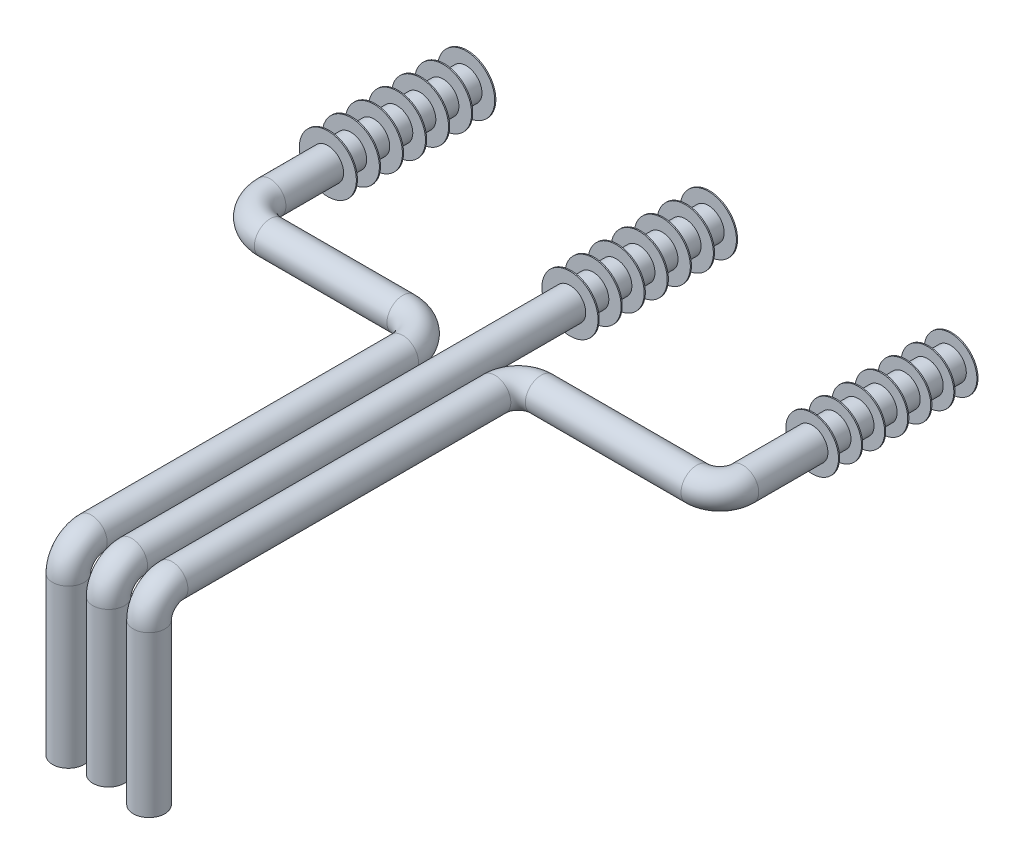
SolidWorks part; units mm, degrees
ref_plane "Alzado" through (0, 0, 0) normal (0, 0, 1) x (1, 0, 0)
ref_plane "Planta" through (0, 0, 0) normal (0, 1, 0) x (1, 0, 0)
ref_plane "Vista lateral" through (0, 0, 0) normal (1, 0, 0) x (0, 0, -1)
sketch "Croquis1" plane through (0, 0, 0) normal (0, 0, 1) x (1, 0, 0)
  line L0 (0, 0) -> (210, 0) construction
  line L1 (210, 0) -> (420, 0) construction
  circle A0 centre (0, 0) radius 13.7
  circle A1 centre (210, 0) radius 13.7
  circle A2 centre (210, 0) radius 13.7
  dimension "D1" = 27.4
  dimension "D3" = 27.4
  dimension "D2" = 210
  dimension "D4" = 210
sketch3d "Croquis3D1"
  line L0 (0, 0, 0) -> (0, 0, 170)
  line L1 (30, 0, 200) -> (145.0002, 0, 200)
  line L2 (175.0002, 0, 230) -> (175.0002, 0, 500)
  line L3 (175.0002, -20, 520) -> (175.0002, -156.8001, 520)
  arc A0 (0, 0, 170) -> (30, 0, 200) centre (30, 0, 170) ccw
  arc A1 (145.0002, 0, 200) -> (175.0002, 0, 230) centre (145.0002, 0, 230) ccw
  arc A2 (175.0002, 0, 500) -> (175.0002, -20, 520) centre (175.0002, -20, 500) ccw
  point P10 (0, 0, 200)
  point P11 (30, 30, 170)
  point P14 (175.0002, 0, 200)
  point P15 (145.0002, -30, 230)
  point P19 (175.0002, 0, 520)
  point P20 (195.0002, -20, 500)
  dimension "D1" = 30
  dimension "D2" = 20
  dimension "D3" = 175.0002
  dimension "D4" = 200
  dimension "D5" = 320
sweep "Barrer5" add path "Croquis3D1" circular profile diameter 27.4 parameters "D3"=27.4
sketch "Croquis14" plane through (0, 0, 0) normal (0, 0, 1) x (1, 0, 0)
  circle A0 centre (210, 0) radius 13.7
sketch3d "Croquis3D2"
  line L0 (210, 0, 0) -> (210, 0, 499.997)
  line L1 (210, -20, 519.997) -> (210, -153.4253, 519.997)
  arc A0 (210, 0, 499.997) -> (210, -20, 519.997) centre (210, -20, 499.997) ccw
  point P8 (210, 0, 519.997)
  point P9 (230, -20, 499.997)
  dimension "D1" = 20
  dimension "D2" = 519.997
sweep "Barrer6" add path "Croquis3D2" circular profile diameter 27.4 parameters "D3"=27.4
sketch "Croquis41" plane through (0, 0, 0) normal (0, 0, -1) x (-1, 0, 0)
  circle A0 centre (-420, 0) radius 13.7
  dimension "D1" = 27.4
sketch3d "Croquis3D3"
  line L0 (420, 0, 0) -> (420, 0, 180)
  line L1 (400, 0, 200) -> (264.998, 0, 200)
  line L2 (244.998, 0, 220) -> (244.998, 0, 500)
  line L3 (244.998, -20, 520) -> (244.998, -158.8149, 520)
  arc A0 (244.998, 0, 500) -> (244.998, -20, 520) centre (244.998, -20, 500) ccw
  arc A1 (420, 0, 180) -> (400, 0, 200) centre (400, 0, 180) ccw
  arc A2 (264.998, 0, 200) -> (244.998, 0, 220) centre (264.998, 0, 220) ccw
  point P8 (244.998, 0, 520)
  point P9 (264.998, -20, 500)
  point P12 (420, 0, 200)
  point P13 (400, -20, 180)
  point P16 (244.998, 0, 200)
  point P17 (264.998, 20, 220)
  dimension "D1" = 20
  dimension "D2" = 175.002
  dimension "D3" = 200
  dimension "D4" = 320
sweep "Barrer7" add profiles "Croquis41" path "Croquis3D3"
sketch "Croquis62" plane through (0, 0, 0) normal (0, 0, -1) x (-1, 0, 0)
  circle A0 centre (-420, 0) radius 22.8702
  circle A1 centre (-210, 0) radius 24.3657
  circle A2 centre (0, 0) radius 24.738
extrude "Saliente-Extruir1" add sketch "Croquis62" along normal blind 1
pattern_linear "MatrizL1" count 7 spacing 20 along (0, 0, 1) of "Saliente-Extruir1"
sketch "Croquis63" plane through (0, -158.8149, 0) normal (0, -1, 0) x (1, 0, 0)
  line L0 (231.298, 520) -> (258.698, 520) construction
  line L1 (258.698, 520) -> (244.998, 520) construction
  line L2 (244.998, 520) -> (244.998, 533.7) construction
  circle A0 centre (244.998, 520) radius 13.7 construction
ref_plane "Plano1" through (0, 0, 520) normal (0, 0, -1) x (1, 0, 0)
sketch "Croquis64" plane through (0, -156.8001, 0) normal (0, -1, 0) x (1, 0, 0)
  circle A0 centre (175.0002, 520) radius 13.7
  circle A1 centre (210, 519.997) radius 13.7
  circle A2 centre (244.998, 520) radius 13.7
sketch3d "Croquis3D4"
  line L0 (175.0002, -156.8001, 520) -> (175.0002, -328.3979, 520)
  line L1 (175.0002, -348.3979, 540) -> (175.0002, -348.3979, 534.5871)
  line L2 (175.0002, -368.3979, 554.5871) -> (175.0002, -536.3535, 554.5871)
  arc A0 (175.0002, -348.3979, 534.5871) -> (175.0002, -368.3979, 554.5871) centre (175.0002, -368.3979, 534.5871) ccw
  arc A1 (175.0002, -328.3979, 520) -> (175.0002, -348.3979, 540) centre (175.0002, -328.3979, 540) ccw
  point P7 (175.0002, -348.3979, 554.5871)
  point P8 (195.0002, -368.3979, 534.5871)
  point P11 (175.0002, -348.3979, 520)
  point P12 (155.0002, -328.3979, 540)
  dimension "D1" = 20
